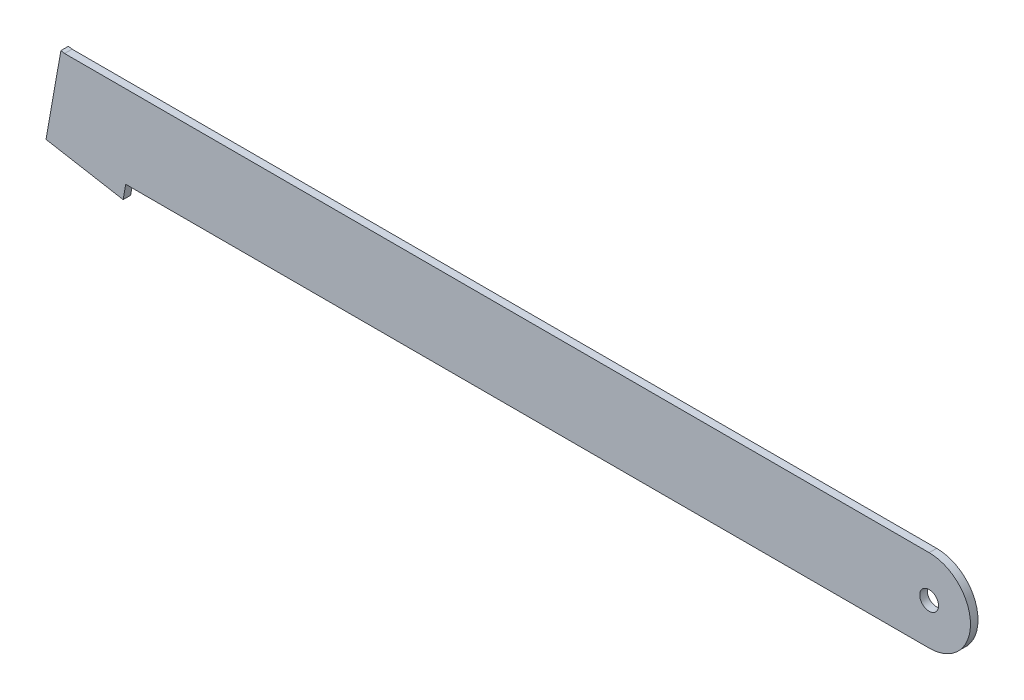
SolidWorks part; units mm, degrees
ref_plane "Front" through (0, 0, 0) normal (0, 0, 1) x (1, 0, 0)
ref_plane "Top" through (0, 0, 0) normal (0, 1, 0) x (1, 0, 0)
ref_plane "Right" through (0, 0, 0) normal (1, 0, 0) x (0, 0, -1)
sketch "Sketch1" plane through (0, 0, 0) normal (0, 0, 1) x (1, 0, 0)
  line L0 (-2300, 110) -> (-2309.8481, 111.7365)
  line L1 (0, 110) -> (-2300, 110)
  line L3 (0, -110) -> (-2137.4035, -110)
  line L5 (-2309.8481, 111.7365) -> (-2344.2096, -83.1373)
  line L10 (-2344.2096, -83.1373) -> (-2349.419, -112.6815)
  line L11 (-2137.4035, -110) -> (-2144.2552, -148.8574)
  line L12 (-2349.419, -112.6815) -> (-2144.2552, -148.8574)
  arc A2 (0, 110) -> (0, -110) centre (0, 0) cw
  circle A3 centre (0, 0) radius 25
  point P0 (0, 0)
  point P9 (0, 0)
  dimension "D2" = 110
  dimension "D9" = 50
  dimension "D1" = 2300
  dimension "D3" = 110
  dimension "D4" = 30
  dimension "D5" = 10
  dimension "D6" = 2344.2096
  dimension "D7" = 197.88
  dimension "D8" = 39.4569
  dimension "D10" = 110
  dimension "D11" = 205.1639
extrude "Boss-Extrude1" add sketch "Sketch1" along normal mid plane 20
